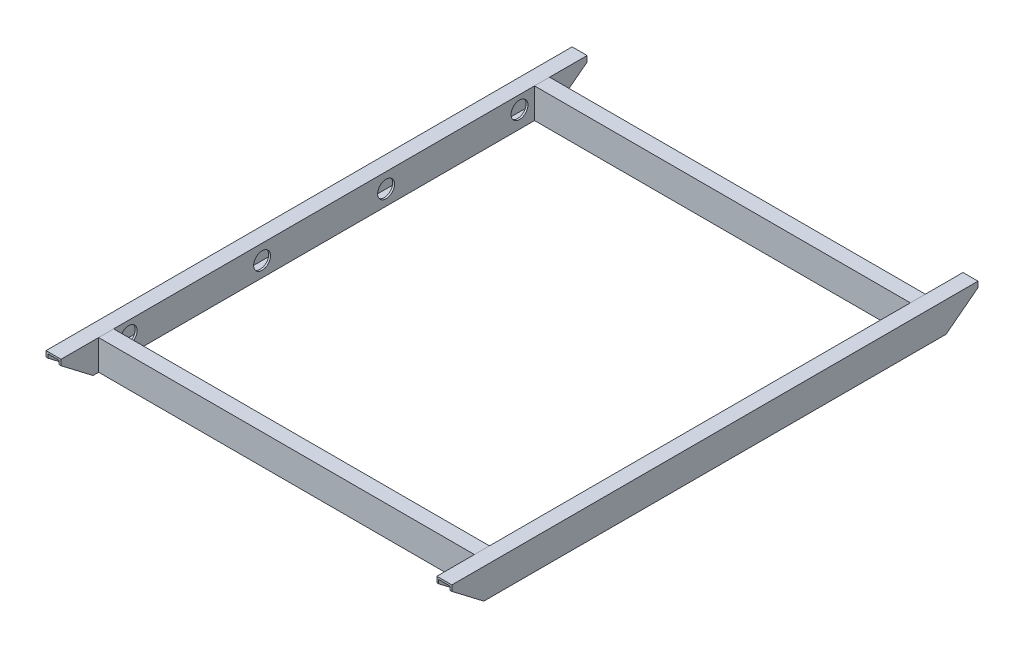
SolidWorks part; units mm, degrees
ref_plane "Front" through (0, 0, 0) normal (0, 0, 1) x (1, 0, 0)
ref_plane "Top" through (0, 0, 0) normal (0, 1, 0) x (1, 0, 0)
ref_plane "Right" through (0, 0, 0) normal (1, 0, 0) x (0, 0, -1)
sketch "Basic Outline" plane through (0, 0, 0) normal (0, 1, 0) x (1, 0, 0)
  line L0 (-330.2, 368.3) -> (330.2, 368.3)
  line L1 (-330.2, -444.5) -> (330.2, -444.5)
  line L2 (-330.2, -444.5) -> (-330.2, 444.5)
  line L3 (-330.2, 444.5) -> (330.2, 444.5)
  line L4 (330.2, -444.5) -> (330.2, 444.5)
  line L5 (-330.2, -444.5) -> (330.2, 444.5) construction
  line L6 (-330.2, 444.5) -> (330.2, -444.5) construction
  line L7 (-330.2, -368.3) -> (330.2, -368.3)
  point P0 (0, 0)
  dimension "D1" = 660.4
  dimension "D2" = 889
  dimension "D3" = 76.2
  dimension "D4" = 76.2
other "Rectangular tube 2 X 1 X 0.125(1)"
ref_plane "Plane2" through (-330.2, 0, 444.5) normal (0, 0, -1) x (0, 1, 0)
sketch "Sketch12" plane through (-330.2, 0, 444.5) normal (0, 0, -1) x (0, 1, 0)
  line L0 (-22.225, -9.525) -> (-22.225, 9.525)
  line L1 (-25.4, -12.7) -> (25.4, -12.7)
  line L2 (-25.4, -12.7) -> (-25.4, 12.7)
  line L3 (-25.4, 12.7) -> (25.4, 12.7)
  line L4 (25.4, -12.7) -> (25.4, 12.7)
  line L5 (-25.4, -12.7) -> (25.4, 12.7) construction
  line L6 (-25.4, 12.7) -> (25.4, -12.7) construction
  line L7 (-22.225, 9.525) -> (22.225, 9.525)
  line L8 (22.225, -9.525) -> (22.225, 9.525)
  line L9 (-22.225, -9.525) -> (22.225, -9.525)
  point P0 (0, 0)
  point P10 (0, 0)
  dimension "D1" = 50.8
  dimension "D2" = 25.4
  dimension "D3" = 3.175
other "Rectangular tube 2 X 1 X 0.125(2)"
ref_plane "Plane4" through (-330.2, 0, -368.3) normal (1, 0, 0) x (0, 1, 0)
sketch "Sketch13" plane through (-330.2, 0, -368.3) normal (1, 0, 0) x (0, 1, 0)
  line L0 (-22.225, -9.525) -> (-22.225, 9.525)
  line L1 (-25.4, -12.7) -> (25.4, -12.7)
  line L2 (-25.4, -12.7) -> (-25.4, 12.7)
  line L3 (-25.4, 12.7) -> (25.4, 12.7)
  line L4 (25.4, -12.7) -> (25.4, 12.7)
  line L5 (-25.4, -12.7) -> (25.4, 12.7) construction
  line L6 (-25.4, 12.7) -> (25.4, -12.7) construction
  line L7 (-22.225, 9.525) -> (22.225, 9.525)
  line L8 (22.225, -9.525) -> (22.225, 9.525)
  line L9 (-22.225, -9.525) -> (22.225, -9.525)
  point P0 (0, 0)
  point P10 (0, 0)
  dimension "D1" = 50.8
  dimension "D2" = 25.4
  dimension "D3" = 3.175
other "Trim/Extend1"
sketch "Sketch14" plane through (-342.9, 0, 0) normal (-1, 0, 0) x (0, 0, 1)
  line L0 (-444.5, 15.875) -> (-390.525, -25.4)
  line L1 (-444.5, -25.4) -> (-444.5, 25.4) construction
  line L2 (-444.5, -25.4) -> (444.5, -25.4) construction
  line L3 (-390.525, -25.4) -> (-444.5, -25.4)
  line L4 (-444.5, -25.4) -> (-444.5, 15.875)
  line L5 (-444.5, 25.4) -> (444.5, 25.4) construction
  line L6 (-381, 25.4) -> (-381, -25.4) construction
  line L7 (0, 25.4) -> (0, -25.4) construction
  line L8 (444.5, -25.4) -> (444.5, 15.875)
  line L9 (390.525, -25.4) -> (444.5, -25.4)
  line L10 (444.5, 15.875) -> (390.525, -25.4)
  dimension "D1" = 9.525
  dimension "D2" = 9.525
extrude "Cut-Extrude1" cut sketch "Sketch14" against normal through all
sketch "Sketch15" plane through (-317.5, 0, 0) normal (1, 0, 0) x (0, 0, -1)
  line L0 (330.2, -25.4) -> (330.2, 25.4) construction
  line L1 (390.525, -25.4) -> (-390.525, -25.4) construction
  line L2 (444.5, 25.4) -> (-444.5, 25.4) construction
  line L3 (444.5, 20.6375) -> (330.2, 20.6375) construction
  line L4 (444.5, 25.4) -> (444.5, 15.875) construction
  line L5 (330.2, 0) -> (287.6741, 0) construction
  line L6 (104.775, 25.4) -> (104.775, -25.4) construction
  line L7 (330.2, -20.9695) -> (104.775, -20.9695) construction
  line L8 (0, 25.4) -> (0, -25.4) construction
  circle A0 centre (330.2, 3.175) radius 14.2875
  circle A1 centre (104.775, 0) radius 14.2875
  circle A2 centre (-330.2, 3.175) radius 14.2875
  circle A3 centre (-104.775, 0) radius 14.2875
  dimension "D2" = 28.575
  dimension "D5" = 28.575
  dimension "D1" = 114.3
  dimension "D3" = 3.175
  dimension "D4" = 225.425
extrude "Cut-Extrude2" cut sketch "Sketch15" against normal through all
